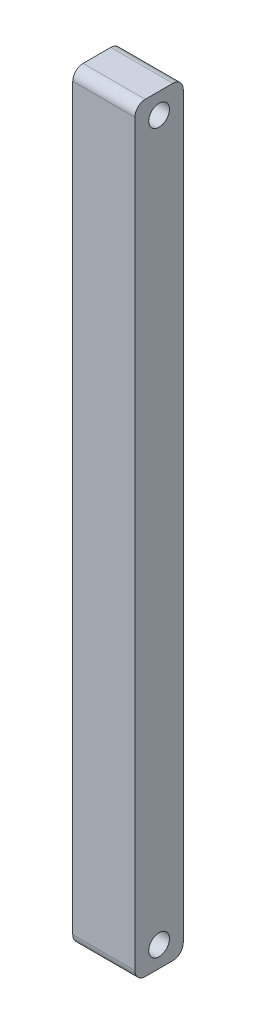
SolidWorks part; units mm, degrees
ref_plane "Front Plane" through (0, 0, 0) normal (0, 0, 1) x (1, 0, 0)
ref_plane "Top Plane" through (0, 0, 0) normal (0, 1, 0) x (1, 0, 0)
ref_plane "Right Plane" through (0, 0, 0) normal (1, 0, 0) x (0, 0, -1)
sketch "Sketch1" plane through (0, 0, 0) normal (0, 0, 1) x (1, 0, 0)
  line L0 (-0.5452, -0.9378) -> (-0.5452, 109.0622)
  line L1 (-0.5452, -0.9378) -> (8.4548, -0.9378)
  line L2 (-0.5452, 109.0622) -> (8.4548, 109.0622)
  line L3 (8.4548, -0.9378) -> (8.4548, 109.0622)
  dimension "D1" = 110
  dimension "D2" = 9
extrude "Boss-Extrude2" add sketch "Sketch1" along normal blind 7
sketch "Sketch4" plane through (8.4548, 0, 0) normal (1, 0, 0) x (0, 0, -1)
  line L0 (-3.5, -0.9378) -> (-3.5, 21.4889) construction
  line L1 (-7, -0.9378) -> (0, -0.9378) construction
  line L2 (-3.5, 0.5622) -> (-13.592, 0.5622) construction
  circle A0 centre (-3.5, 2.0622) radius 1.5
  dimension "D1" = 3
  dimension "D2" = 1.5
extrude "Cut-Extrude2" cut sketch "Sketch4" against normal through all
sketch "Sketch6" plane through (8.4548, 0, 0) normal (1, 0, 0) x (0, 0, -1)
  circle A0 centre (-3.5, 106.0622) radius 1.5
  dimension "D1" = 3
extrude "Cut-Extrude4" cut sketch "Sketch6" against normal through all
fillet "Fillet1" radius 1.5 2 edges at (3.9548, 109.0622, 0) (3.9548, 109.0622, 7)
fillet "Fillet2" radius 1.5 2 edges at (3.9548, -0.9378, 0) (3.9548, -0.9378, 7)
